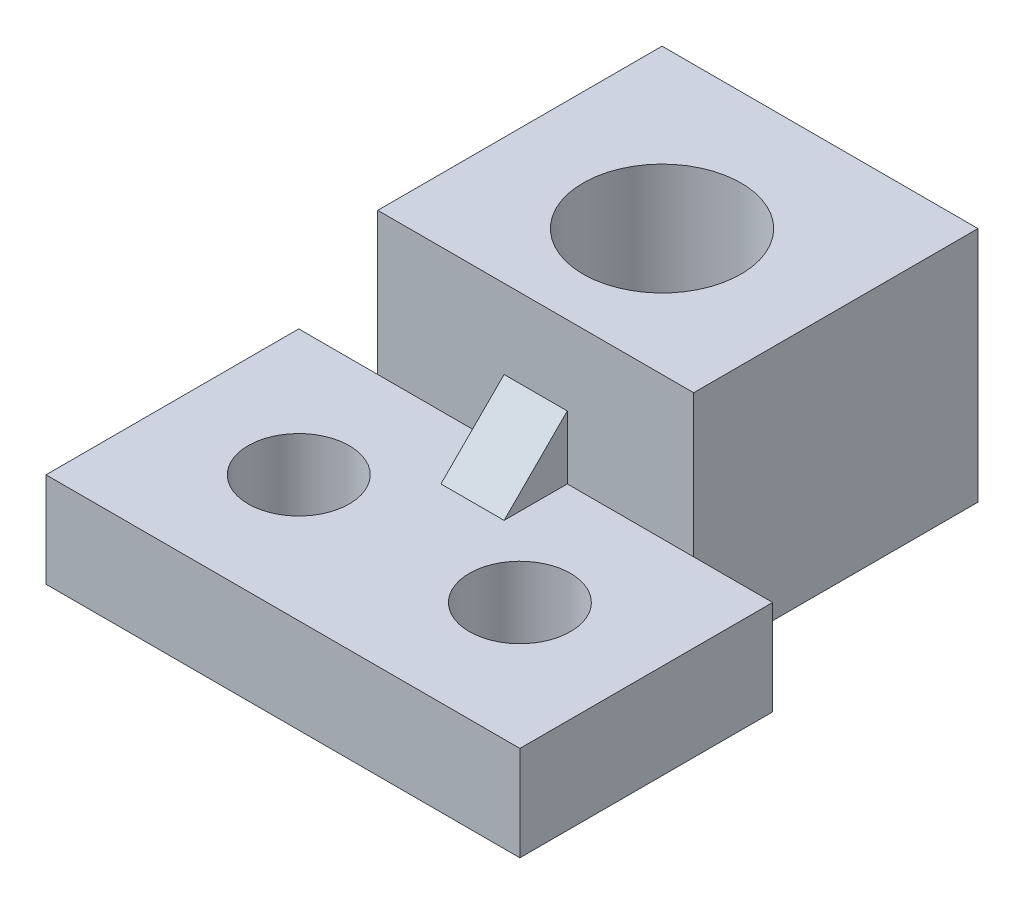
SolidWorks part; units mm, degrees
ref_plane "Front Plane" through (0, 0, 0) normal (0, 0, 1) x (1, 0, 0)
ref_plane "Top Plane" through (0, 0, 0) normal (0, 1, 0) x (1, 0, 0)
ref_plane "Right Plane" through (0, 0, 0) normal (1, 0, 0) x (0, 0, -1)
sketch "Sketch1" plane through (0, 0, 0) normal (0, 1, 0) x (1, 0, 0)
  line L5 (-7.5, 2.9151) -> (7.5, 2.9151)
  line L6 (-7.5, 2.9151) -> (-7.5, -5.0849)
  line L7 (-7.5, -5.0849) -> (7.5, -5.0849)
  line L8 (7.5, 2.9151) -> (7.5, -5.0849)
  circle A0 centre (-3.5, -1.0849) radius 1.6
  circle A1 centre (3.5, -1.0849) radius 1.6
  point P8 (0, 2.9151)
  dimension "D1" = 3.2
  dimension "D2" = 7
  dimension "D3" = 4
  dimension "D4" = 4
  dimension "D5" = 4
  dimension "D6" = 4
extrude "Boss-Extrude1" add sketch "Sketch1" along normal blind 3
sketch "Sketch2" plane through (0, 0, 0) normal (0, 1, 0) x (1, 0, 0)
  line L0 (7.5, 2.9151) -> (-7.5, 2.9151) construction
  line L1 (-5, 2.9151) -> (5, 2.9151)
  line L2 (-5, 2.9151) -> (-5, 11.9151)
  line L3 (-5, 11.9151) -> (5, 11.9151)
  line L4 (5, 2.9151) -> (5, 11.9151)
  line L5 (-7.5, -5.0849) -> (7.5, -5.0849) construction
  circle A0 centre (0, 6.9151) radius 2.5
  point P8 (0, 0)
  point P11 (0, -5.0849)
  dimension "D5" = 4
  dimension "D1" = 5
  dimension "D2" = 5
  dimension "D3" = 5
  dimension "D4" = 5
extrude "Boss-Extrude2" add sketch "Sketch2" along normal blind 7.5
sketch "Sketch4" plane through (0, 0, 0) normal (1, 0, 0) x (0, 0, -1)
  line L0 (2.9151, 5) -> (0.9151, 3)
  line L1 (2.9151, 7.5) -> (2.9151, 3) construction
  line L2 (-5.0849, 3) -> (2.9151, 3) construction
  line L3 (0.9151, 3) -> (2.9151, 3)
  line L4 (2.9151, 3) -> (2.9151, 5)
  dimension "D1" = 2
  dimension "D2" = 2
extrude "Boss-Extrude3" add sketch "Sketch4" along normal mid plane 2
equation "\"padding\"=4"
equation "\"D3@Sketch1\"=\"padding\""
equation "\"D4@Sketch1\"=\"padding\""
equation "\"D5@Sketch1\"=\"padding\""
equation "\"D6@Sketch1\"=\"padding\""
equation "\"risingpadding\"=5"
equation "\"D2@Sketch2\"=\"risingpadding\""
equation "\"D3@Sketch2\"=\"risingpadding\""
equation "\"D4@Sketch2\"=\"risingpadding\""
equation "\"D5@Sketch2\"=\"padding\""
